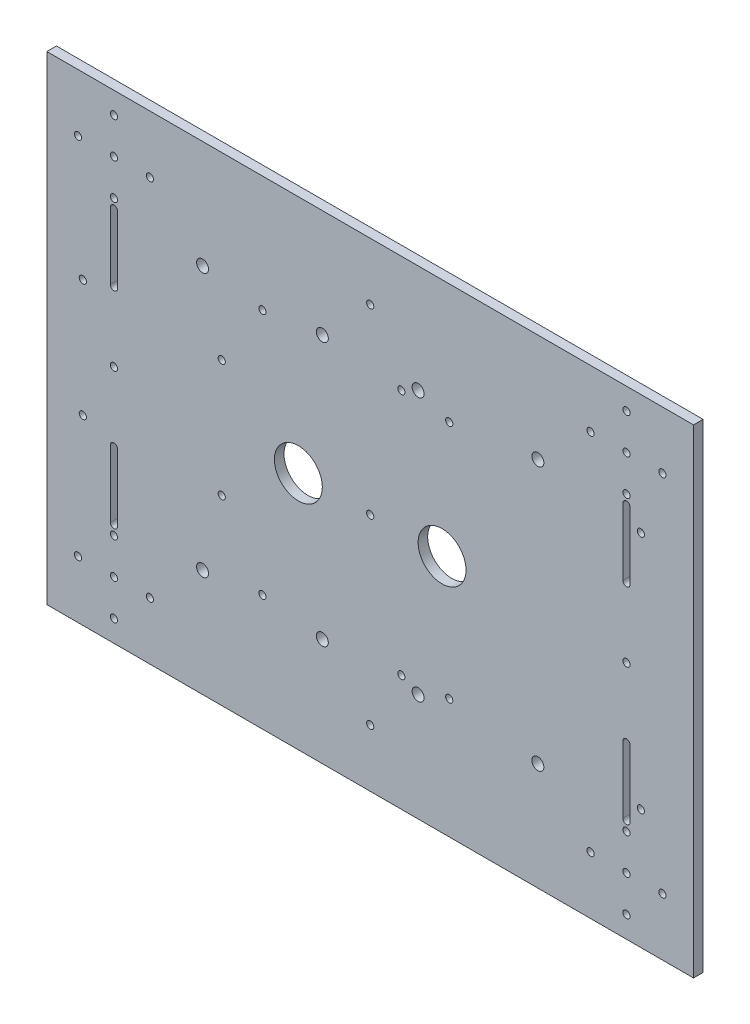
SolidWorks part; units mm, degrees
material "Acrylic (Medium-high impact)"
ref_plane "Front Plane" through (0, 0, 0) normal (0, 0, 1) x (1, 0, 0)
ref_plane "Top Plane" through (0, 0, 0) normal (0, 1, 0) x (1, 0, 0)
ref_plane "Right Plane" through (0, 0, 0) normal (1, 0, 0) x (0, 0, -1)
sketch "Sketch1" plane through (0, 0, 0) normal (0, 0, 1) x (1, 0, 0)
  line L0 (4.9015, 38.8667) -> (94.9015, 38.8667) construction
  line L1 (-60.0985, 83.8667) -> (209.9015, 83.8667)
  line L2 (-60.0985, 83.8667) -> (-60.0985, -116.1333)
  line L3 (-60.0985, -116.1333) -> (209.9015, -116.1333)
  line L4 (209.9015, 83.8667) -> (209.9015, -116.1333)
  line L5 (-17.0985, -92.1333) -> (196.9015, -92.1333) construction
  line L6 (-17.0985, -92.1333) -> (-17.0985, 59.8667) construction
  line L7 (74.9015, -16.1333) -> (181.9015, -16.1333) construction
  line L8 (74.9015, -16.1333) -> (-32.0985, -16.1333) construction
  line L9 (183.4015, -45.1333) -> (183.4015, -73.1333)
  line L10 (-33.5985, -45.1333) -> (-33.5985, -73.1333)
  line L11 (180.4015, -45.1333) -> (180.4015, -73.1333)
  line L12 (-30.5985, -45.1333) -> (-30.5985, -73.1333)
  line L13 (-33.5985, 40.8667) -> (-33.5985, 12.8667)
  line L14 (-30.5985, 40.8667) -> (-30.5985, 12.8667)
  line L15 (180.4015, 40.8667) -> (180.4015, 12.8667)
  line L16 (183.4015, 40.8667) -> (183.4015, 12.8667)
  circle A0 centre (-32.0985, -92.1333) radius 1.5
  circle A1 centre (-17.0985, -92.1333) radius 1.5
  circle A2 centre (-32.0985, -107.1333) radius 1.5
  circle A3 centre (-47.0985, -92.1333) radius 1.5
  circle A4 centre (-32.0985, -77.1333) radius 1.5
  circle A5 centre (74.9015, -16.1333) radius 1.5
  circle A6 centre (196.9015, -92.1333) radius 1.5
  circle A7 centre (181.9015, -77.1333) radius 1.5
  circle A8 centre (181.9015, -92.1333) radius 1.5
  circle A9 centre (181.9015, -107.1333) radius 1.5
  circle A10 centre (166.9015, -92.1333) radius 1.5
  circle A11 centre (196.9015, 59.8667) radius 1.5
  circle A12 centre (181.9015, 74.8667) radius 1.5
  circle A13 centre (181.9015, 59.8667) radius 1.5
  circle A14 centre (181.9015, 44.8667) radius 1.5
  circle A15 centre (166.9015, 59.8667) radius 1.5
  circle A16 centre (-17.0985, 59.8667) radius 1.5
  circle A17 centre (-32.0985, 74.8667) radius 1.5
  circle A18 centre (-32.0985, 59.8667) radius 1.5
  circle A19 centre (-32.0985, 44.8667) radius 1.5
  circle A20 centre (-47.0985, 59.8667) radius 1.5
  circle A21 centre (181.9015, -16.1333) radius 1.5
  circle A22 centre (181.9015, 59.8667) radius 1.5
  circle A23 centre (74.9015, 59.8667) radius 1.5
  circle A24 centre (104.9015, -16.1333) radius 10
  circle A25 centre (44.9015, -16.1333) radius 10
  circle A26 centre (-32.0985, -16.1333) radius 1.5
  circle A27 centre (-32.0985, -92.1333) radius 1.5 [skipped]
  circle A28 centre (74.9015, -92.1333) radius 1.5
  circle A29 centre (4.9015, 38.8667) radius 2.5
  circle A30 centre (54.9015, 38.8667) radius 2.5
  circle A31 centre (94.9015, 38.8667) radius 2.5
  circle A32 centre (144.9015, 38.8667) radius 2.5
  circle A33 centre (94.9015, -71.1333) radius 2.5
  circle A34 centre (144.9015, -71.1333) radius 2.5
  circle A35 centre (4.9015, -71.1333) radius 2.5
  circle A36 centre (54.9015, -71.1333) radius 2.5
  circle A37 centre (-45.0985, 8.8667) radius 1.5
  circle A38 centre (12.9015, 8.8667) radius 1.5
  circle A39 centre (12.9015, -40.1333) radius 1.5
  circle A40 centre (-45.0985, -40.1333) radius 1.5
  circle A41 centre (29.9015, 35.3667) radius 1.5
  circle A42 centre (87.9015, 35.3667) radius 1.5
  circle A43 centre (87.9015, -67.6333) radius 1.5
  circle A44 centre (29.9015, -67.6333) radius 1.5
  circle A45 centre (107.9015, 33.8667) radius 1.5
  circle A46 centre (187.9015, 33.8667) radius 1.5
  circle A47 centre (187.9015, -66.1333) radius 1.5
  circle A48 centre (107.9015, -66.1333) radius 1.5
  arc A49 (180.4015, -73.1333) -> (183.4015, -73.1333) centre (181.9015, -73.1333) ccw
  arc A50 (183.4015, -45.1333) -> (180.4015, -45.1333) centre (181.9015, -45.1333) ccw
  arc A51 (-33.5985, -73.1333) -> (-30.5985, -73.1333) centre (-32.0985, -73.1333) ccw
  arc A52 (-30.5985, -45.1333) -> (-33.5985, -45.1333) centre (-32.0985, -45.1333) ccw
  arc A53 (-33.5985, 12.8667) -> (-30.5985, 12.8667) centre (-32.0985, 12.8667) ccw
  arc A54 (-30.5985, 40.8667) -> (-33.5985, 40.8667) centre (-32.0985, 40.8667) ccw
  arc A55 (180.4015, 12.8667) -> (183.4015, 12.8667) centre (181.9015, 12.8667) ccw
  arc A56 (183.4015, 40.8667) -> (180.4015, 40.8667) centre (181.9015, 40.8667) ccw
  point P28 (-32.0985, -92.1333)
  dimension "D2" = 60
  dimension "D3" = 24
  dimension "D4" = 2
  dimension "D5" = 15
  dimension "D9" = 2
  dimension "D7" = 100
  dimension "D8" = 2
  dimension "D16" = 2
  dimension "D21" = 50
  dimension "D23" = 65
  dimension "D27" = 76
  dimension "D28" = 107
  dimension "D29" = 2
  dimension "D32" = 15
  dimension "D33" = 2
  dimension "D37" = 2
  dimension "D39" = 50
  dimension "D40" = 20
  dimension "D42" = 28
  dimension "D43" = 2
  dimension "D10" = 9
  dimension "D11" = 28
  dimension "D12" = 200
  dimension "D13" = 270
  dimension "D14" = 214
  dimension "D15" = 152
  dimension "D17" = 107
  dimension "D20" = 107
  dimension "D22" = 45
  dimension "D24" = 2
  dimension "D26" = 90
  dimension "D31" = 75
  dimension "D36" = 48.5
  dimension "D41" = 4
  dimension "D45" = 80
  dimension "D18" = 2
  dimension "D19" = 2
  dimension "D25" = 2
  dimension "D34" = 2
  dimension "D38" = 2
  dimension "D44" = 2
  dimension "D30" = 2
  dimension "D6" = 4
extrude "Boss-Extrude1" add sketch "Sketch1" along normal blind 4 contours L4 L1 L2 L3 A28 A26 A0 A1 A2 A3 A4 A5 A6 A7 A8 A9 A10 A11 A12 A13 A14 A15 A16 A17 A18 A19 A20
